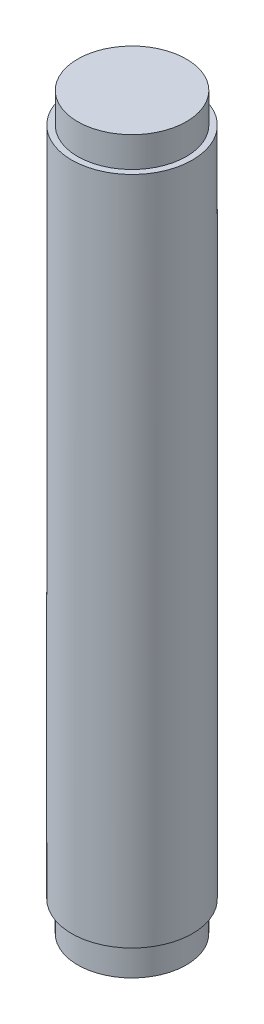
SolidWorks part; units mm, degrees
ref_plane "Front Plane" through (0, 0, 0) normal (0, 0, 1) x (1, 0, 0)
ref_plane "Top Plane" through (0, 0, 0) normal (0, 1, 0) x (1, 0, 0)
ref_plane "Right Plane" through (0, 0, 0) normal (1, 0, 0) x (0, 0, -1)
sketch "Sketch1" plane through (0, 0, 0) normal (0, 1, 0) x (1, 0, 0)
  circle A0 centre (0, 0) radius 5
extrude "Boss-Extrude1" add sketch "Sketch1" along normal blind 60.5
sketch "Sketch24" plane through (0, 0, 0) normal (0, -1, 0) x (-1, 0, 0)
  circle A0 centre (0, 0) radius 5
  circle A1 centre (0, 0) radius 4.5
  dimension "D1" = 0.5
extrude "Cut-Extrude3" cut sketch "Sketch24" against normal blind 2.5
sketch "Sketch25" plane through (0, 60.5, 0) normal (0, 1, 0) x (1, 0, 0)
  circle A0 centre (0, 0) radius 5
  circle A1 centre (0, 0) radius 4.5
  dimension "D1" = 0.5
extrude "Cut-Extrude4" cut sketch "Sketch25" against normal blind 2.5
